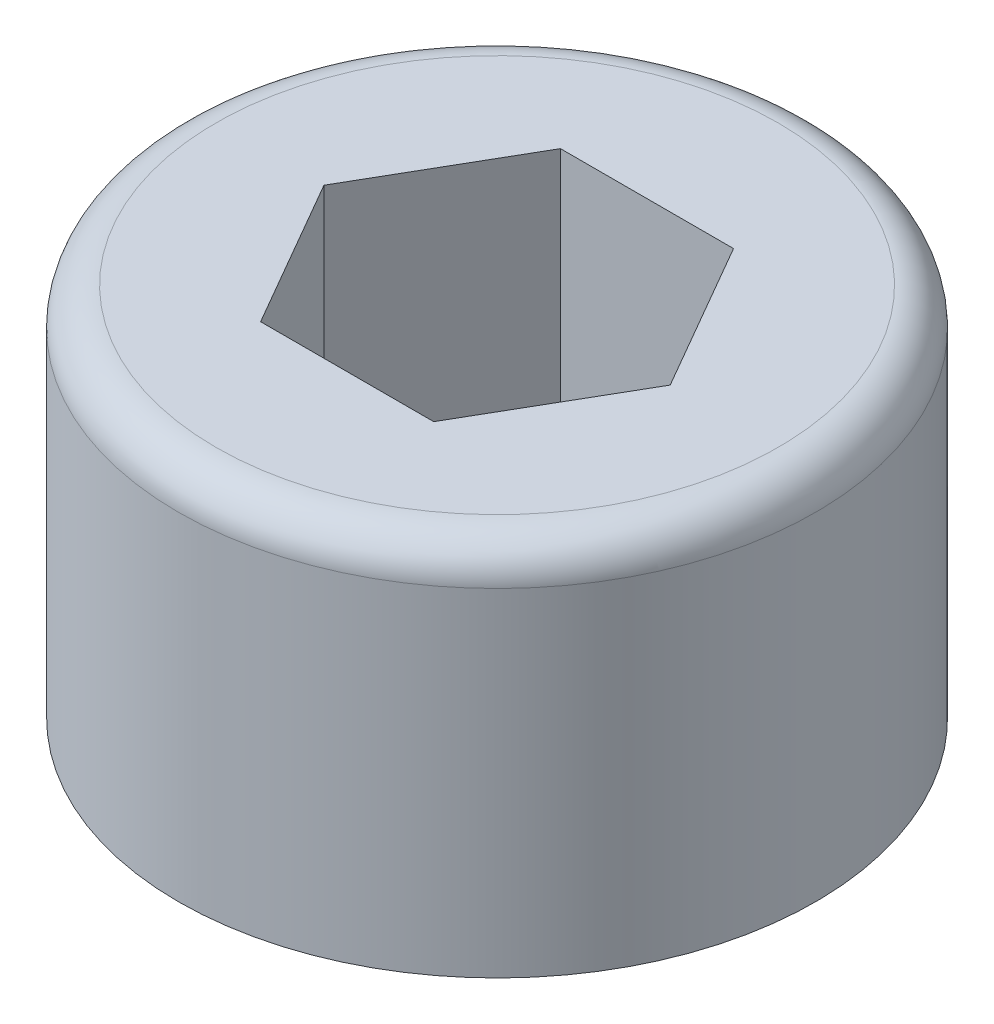
SolidWorks part; units mm, degrees
ref_plane "Front Plane" through (0, 0, 0) normal (0, 0, 1) x (1, 0, 0)
ref_plane "Top Plane" through (0, 0, 0) normal (0, 1, 0) x (1, 0, 0)
ref_plane "Right Plane" through (0, 0, 0) normal (1, 0, 0) x (0, 0, -1)
sketch "Sketch1" plane through (0, 0, 0) normal (0, 1, 0) x (1, 0, 0)
  circle A0 centre (0, 0) radius 4.25
  dimension "D1" = 8.5
extrude "Boss-Extrude1" add sketch "Sketch1" along normal blind 5
sketch "Sketch2" plane through (0, 5, 0) normal (0, 1, 0) x (1, 0, 0)
  line L1 (-2.3094, 0) -> (-1.1547, -2)
  line L2 (-1.1547, -2) -> (1.1547, -2)
  line L3 (1.1547, -2) -> (2.3094, 0)
  line L4 (2.3094, 0) -> (1.1547, 2)
  line L5 (1.1547, 2) -> (-1.1547, 2)
  line L6 (-1.1547, 2) -> (-2.3094, 0)
  circle A0 centre (0, 0) radius 2 construction
  dimension "D1" = 4
extrude "Cut-Extrude1" cut sketch "Sketch2" against normal blind 3
fillet "Fillet1" radius 0.5 1 edges at (0, 5, 4.25)
